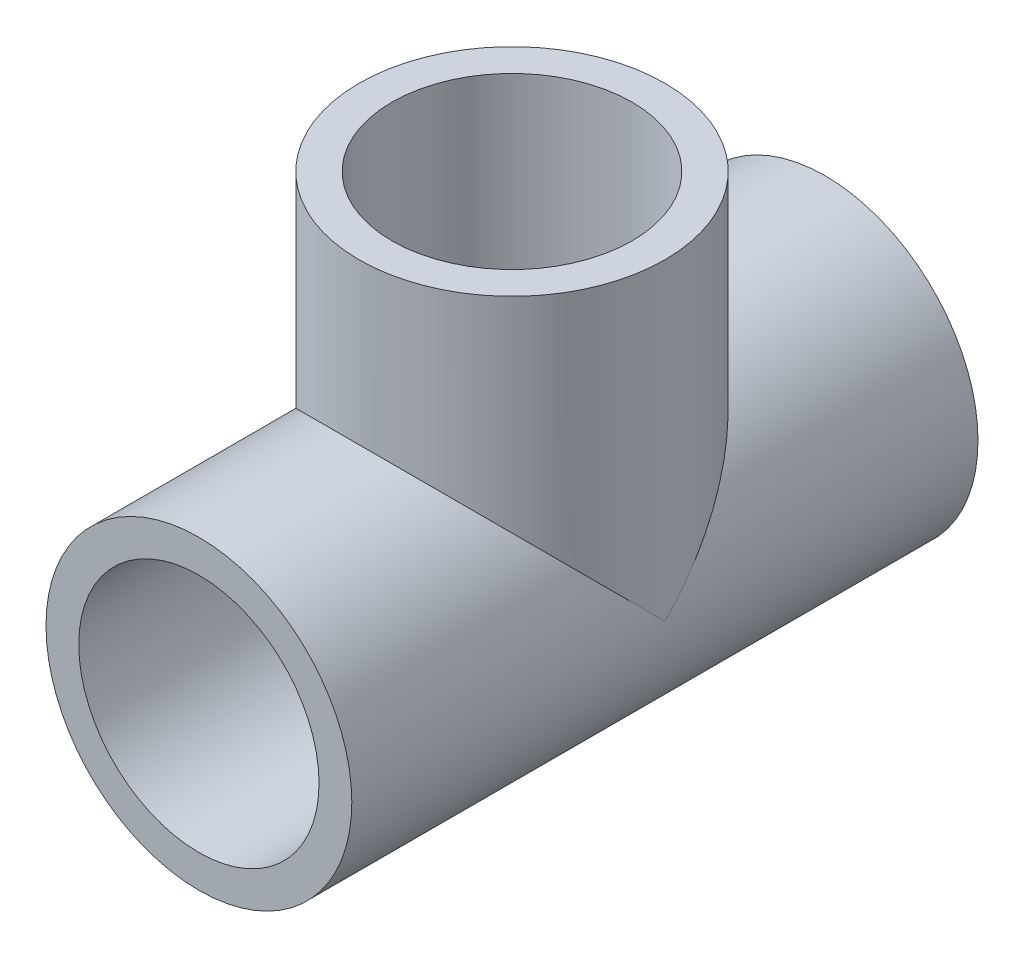
SolidWorks part; units mm, degrees
ref_plane "Front Plane" through (0, 0, 0) normal (0, 0, 1) x (1, 0, 0)
ref_plane "Top Plane" through (0, 0, 0) normal (0, 1, 0) x (1, 0, 0)
ref_plane "Right Plane" through (0, 0, 0) normal (1, 0, 0) x (0, 0, -1)
sketch "Sketch1" plane through (0, 0, 0) normal (0, 1, 0) x (1, 0, 0)
  line L0 (16.6687, 34.1313) -> (0, 34.1313)
  line L1 (0, 34.1313) -> (0, -34.1313)
  line L2 (0, -34.1313) -> (16.6687, -34.1313)
  line L3 (16.6687, -34.1313) -> (16.6687, 34.1313)
  line L4 (0, -118.244) -> (0, 82.7642) construction
  dimension "D1" = 68.2625
  dimension "D2" = 16.6687
revolve "Revolve1" add sketch "Sketch1" angle 360 about L4
sketch "Sketch2" plane through (0, 0, 0) normal (0, 0, 1) x (1, 0, 0)
  line L0 (0, 34.1313) -> (-16.6687, 34.1313)
  line L1 (-16.6687, 34.1313) -> (-16.6687, 0)
  line L2 (-16.6687, 0) -> (0, 0)
  line L3 (0, 0) -> (0, 34.1313)
  line L4 (0, 0) -> (0, 34.1313) construction
  line L5 (0, 0) -> (0, -16.6687) construction
  circle A0 centre (0, 0) radius 16.6687 construction
  dimension "D1" = 50.8
revolve "Revolve2" add sketch "Sketch2" angle 360 about L4
sketch "Sketch7" plane through (0, 0, 34.1313) normal (0, 0, 1) x (1, 0, 0)
  circle A0 centre (0, 0) radius 12.7
  dimension "D1" = 25.4
extrude "Cut-Extrude1" cut sketch "Sketch7" against normal through all
sketch "Sketch8" plane through (0, 34.1313, 0) normal (0, 1, 0) x (1, 0, 0)
  circle A0 centre (0, 0) radius 12.7
  dimension "D1" = 25.4
extrude "Cut-Extrude2" cut sketch "Sketch8" against normal up to next
sketch "Sketch9" plane through (0, 0, 34.1313) normal (0, 0, 1) x (1, 0, 0)
  circle A0 centre (0, 0) radius 13.0969
  dimension "D1" = 26.1937
extrude "Cut-Extrude3" cut sketch "Sketch9" against normal blind 19.05 contours A0
sketch "Sketch10" plane through (0, 0, -34.1313) normal (0, 0, -1) x (-1, 0, 0)
  circle A0 centre (0, 0) radius 13.0969
  dimension "D1" = 26.1937
extrude "Cut-Extrude4" cut sketch "Sketch10" against normal blind 19.05
sketch "Sketch11" plane through (0, 34.1313, 0) normal (0, 1, 0) x (1, 0, 0)
  circle A0 centre (0, 0) radius 13.0969
  dimension "D1" = 26.1937
extrude "Cut-Extrude5" cut sketch "Sketch11" against normal blind 19.05
